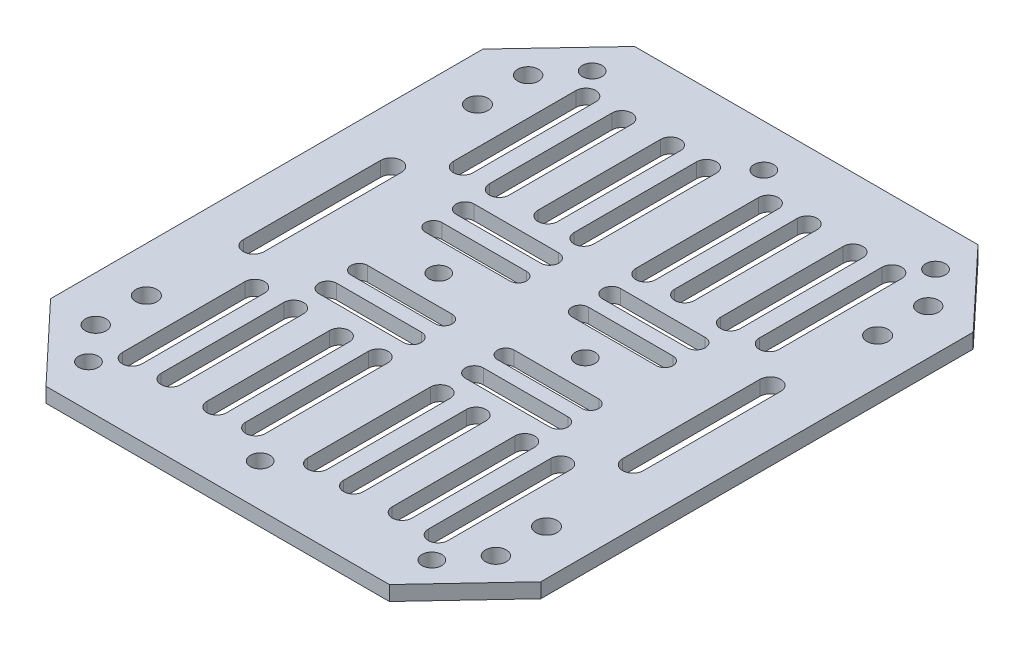
SolidWorks part; units mm, degrees
ref_plane "Front Plane" through (0, 0, 0) normal (0, 0, 1) x (1, 0, 0)
ref_plane "Top Plane" through (0, 0, 0) normal (0, 1, 0) x (1, 0, 0)
ref_plane "Right Plane" through (0, 0, 0) normal (1, 0, 0) x (0, 0, -1)
sketch "Sketch1" plane through (0, 0, 0) normal (0, 1, 0) x (1, 0, 0)
  line L0 (-19.8347, -51.3672) -> (-89.8347, -51.3672)
  line L1 (-104.8347, -35.4409) -> (-104.8347, 52.7065)
  line L2 (-19.8347, 68.6328) -> (-89.8347, 68.6328)
  line L3 (-91.3761, 22.6328) -> (-91.3761, -5.3672)
  line L4 (-95.6191, 22.6328) -> (-95.6191, -5.3672)
  line L5 (-18.2932, 22.6328) -> (-18.2932, -5.3672)
  line L6 (-89.8347, 68.6328) -> (-104.8347, 52.7065)
  line L7 (-89.8347, -51.3672) -> (-104.8347, -35.4409)
  line L8 (-80.4095, -37.3307) -> (-80.4095, -12.3238)
  line L9 (-76.3854, -37.3307) -> (-76.3854, -12.3238)
  line L10 (-88.0384, -37.6182) -> (-88.0384, -12.6112)
  line L11 (-84.0143, -37.6182) -> (-84.0143, -12.6112)
  line L12 (-63.1577, -37.3307) -> (-63.1577, -12.3238)
  line L13 (-59.1336, -37.3307) -> (-59.1336, -12.3238)
  line L14 (-70.7866, -37.6182) -> (-70.7866, -12.6112)
  line L15 (-66.7625, -37.6182) -> (-66.7625, -12.6112)
  line L16 (-61.1456, -0.641) -> (-78.3975, -0.641)
  line L17 (-61.1456, 2.7604) -> (-78.3975, 2.7604)
  line L18 (-61.1456, -7.1978) -> (-78.3975, -7.1978)
  line L19 (-61.1456, -3.5366) -> (-78.3975, -3.5366)
  line L20 (-80.4095, 54.5963) -> (-80.4095, 29.5893)
  line L21 (-76.3854, 54.5963) -> (-76.3854, 29.5893)
  line L22 (-88.0384, 54.8838) -> (-88.0384, 29.8768)
  line L23 (-84.0143, 54.8838) -> (-84.0143, 29.8768)
  line L24 (-63.1577, 54.5963) -> (-63.1577, 29.5893)
  line L25 (-59.1336, 54.5963) -> (-59.1336, 29.5893)
  line L26 (-70.7866, 54.8838) -> (-70.7866, 29.8768)
  line L27 (-66.7625, 54.8838) -> (-66.7625, 29.8768)
  line L28 (-61.1456, 17.9066) -> (-78.3975, 17.9066)
  line L29 (-61.1456, 14.5052) -> (-78.3975, 14.5052)
  line L30 (-61.1456, 24.4634) -> (-78.3975, 24.4634)
  line L31 (-61.1456, 20.8022) -> (-78.3975, 20.8022)
  line L32 (-4.8877, 52.7065) -> (-4.8877, -35.4409)
  line L33 (-29.2598, -37.3307) -> (-29.2598, -12.3238)
  line L34 (-33.2839, -37.3307) -> (-33.2839, -12.3238)
  line L35 (-21.6309, -37.6182) -> (-21.6309, -12.6112)
  line L36 (-25.655, -37.6182) -> (-25.655, -12.6112)
  line L37 (-46.5117, -37.3307) -> (-46.5117, -12.3238)
  line L38 (-50.5358, -37.3307) -> (-50.5358, -12.3238)
  line L39 (-38.8828, -37.6182) -> (-38.8828, -12.6112)
  line L40 (-42.9069, -37.6182) -> (-42.9069, -12.6112)
  line L41 (-48.5237, -0.641) -> (-31.2719, -0.641)
  line L42 (-48.5237, 2.7604) -> (-31.2719, 2.7604)
  line L43 (-48.5237, -7.1978) -> (-31.2719, -7.1978)
  line L44 (-48.5237, -3.5366) -> (-31.2719, -3.5366)
  line L45 (-29.2598, 54.5963) -> (-29.2598, 29.5893)
  line L46 (-33.2839, 54.5963) -> (-33.2839, 29.5893)
  line L47 (-21.6309, 54.8838) -> (-21.6309, 29.8768)
  line L48 (-25.655, 54.8838) -> (-25.655, 29.8768)
  line L49 (-46.5117, 54.5963) -> (-46.5117, 29.5893)
  line L50 (-50.5358, 54.5963) -> (-50.5358, 29.5893)
  line L51 (-38.8828, 54.8838) -> (-38.8828, 29.8768)
  line L52 (-42.9069, 54.8838) -> (-42.9069, 29.8768)
  line L53 (-48.5237, 17.9066) -> (-31.2719, 17.9066)
  line L54 (-48.5237, 14.5052) -> (-31.2719, 14.5052)
  line L55 (-48.5237, 24.4634) -> (-31.2719, 24.4634)
  line L56 (-48.5237, 20.8022) -> (-31.2719, 20.8022)
  line L57 (-14.0502, 22.6328) -> (-14.0502, -5.3672)
  line L58 (-19.8347, -51.3672) -> (-4.8877, -35.4409)
  line L59 (-19.8347, 68.6328) -> (-4.8877, 52.7065)
  arc A0 (-91.3761, 22.6328) -> (-95.6191, 22.6328) centre (-93.4976, 22.6328) ccw
  arc A1 (-95.6191, -5.3672) -> (-91.3761, -5.3672) centre (-93.4976, -5.3672) ccw
  circle A2 centre (-89.8347, -42.7069) radius 2
  circle A3 centre (-54.8347, -42.7069) radius 2
  arc A4 (-80.4095, -37.3307) -> (-76.3854, -37.3307) centre (-78.3975, -37.3307) ccw
  arc A5 (-76.3854, -12.3238) -> (-80.4095, -12.3238) centre (-78.3975, -12.3238) ccw
  arc A6 (-88.0384, -37.6182) -> (-84.0143, -37.6182) centre (-86.0264, -37.6182) ccw
  arc A7 (-84.0143, -12.6112) -> (-88.0384, -12.6112) centre (-86.0264, -12.6112) ccw
  arc A8 (-63.1577, -37.3307) -> (-59.1336, -37.3307) centre (-61.1456, -37.3307) ccw
  arc A9 (-59.1336, -12.3238) -> (-63.1577, -12.3238) centre (-61.1456, -12.3238) ccw
  arc A10 (-70.7866, -37.6182) -> (-66.7625, -37.6182) centre (-68.7745, -37.6182) ccw
  arc A11 (-66.7625, -12.6112) -> (-70.7866, -12.6112) centre (-68.7745, -12.6112) ccw
  arc A12 (-61.1456, -0.641) -> (-61.1456, 2.7604) centre (-61.1456, 1.0597) ccw
  arc A13 (-78.3975, 2.7604) -> (-78.3975, -0.641) centre (-78.3975, 1.0597) ccw
  arc A14 (-61.1456, -7.1978) -> (-61.1456, -3.5366) centre (-61.1456, -5.3672) ccw
  arc A15 (-78.3975, -3.5366) -> (-78.3975, -7.1978) centre (-78.3975, -5.3672) ccw
  arc A16 (-80.4095, 54.5963) -> (-76.3854, 54.5963) centre (-78.3975, 54.5963) cw
  arc A17 (-76.3854, 29.5893) -> (-80.4095, 29.5893) centre (-78.3975, 29.5893) cw
  arc A18 (-88.0384, 54.8838) -> (-84.0143, 54.8838) centre (-86.0264, 54.8838) cw
  arc A19 (-84.0143, 29.8768) -> (-88.0384, 29.8768) centre (-86.0264, 29.8768) cw
  arc A20 (-63.1577, 54.5963) -> (-59.1336, 54.5963) centre (-61.1456, 54.5963) cw
  arc A21 (-59.1336, 29.5893) -> (-63.1577, 29.5893) centre (-61.1456, 29.5893) cw
  arc A22 (-70.7866, 54.8838) -> (-66.7625, 54.8838) centre (-68.7745, 54.8838) cw
  arc A23 (-66.7625, 29.8768) -> (-70.7866, 29.8768) centre (-68.7745, 29.8768) cw
  arc A24 (-61.1456, 17.9066) -> (-61.1456, 14.5052) centre (-61.1456, 16.2059) cw
  arc A25 (-78.3975, 14.5052) -> (-78.3975, 17.9066) centre (-78.3975, 16.2059) cw
  arc A26 (-61.1456, 24.4634) -> (-61.1456, 20.8022) centre (-61.1456, 22.6328) cw
  arc A27 (-78.3975, 20.8022) -> (-78.3975, 24.4634) centre (-78.3975, 22.6328) cw
  circle A28 centre (-89.8347, 59.9725) radius 2
  circle A29 centre (-54.8347, 59.9725) radius 2
  arc A30 (-29.2598, -37.3307) -> (-33.2839, -37.3307) centre (-31.2719, -37.3307) cw
  arc A31 (-33.2839, -12.3238) -> (-29.2598, -12.3238) centre (-31.2719, -12.3238) cw
  arc A32 (-21.6309, -37.6182) -> (-25.655, -37.6182) centre (-23.643, -37.6182) cw
  arc A33 (-25.655, -12.6112) -> (-21.6309, -12.6112) centre (-23.643, -12.6112) cw
  arc A34 (-46.5117, -37.3307) -> (-50.5358, -37.3307) centre (-48.5237, -37.3307) cw
  arc A35 (-50.5358, -12.3238) -> (-46.5117, -12.3238) centre (-48.5237, -12.3238) cw
  arc A36 (-38.8828, -37.6182) -> (-42.9069, -37.6182) centre (-40.8948, -37.6182) cw
  arc A37 (-42.9069, -12.6112) -> (-38.8828, -12.6112) centre (-40.8948, -12.6112) cw
  arc A38 (-48.5237, -0.641) -> (-48.5237, 2.7604) centre (-48.5237, 1.0597) cw
  arc A39 (-31.2719, 2.7604) -> (-31.2719, -0.641) centre (-31.2719, 1.0597) cw
  arc A40 (-48.5237, -7.1978) -> (-48.5237, -3.5366) centre (-48.5237, -5.3672) cw
  arc A41 (-31.2719, -3.5366) -> (-31.2719, -7.1978) centre (-31.2719, -5.3672) cw
  arc A42 (-29.2598, 54.5963) -> (-33.2839, 54.5963) centre (-31.2719, 54.5963) ccw
  arc A43 (-33.2839, 29.5893) -> (-29.2598, 29.5893) centre (-31.2719, 29.5893) ccw
  arc A44 (-21.6309, 54.8838) -> (-25.655, 54.8838) centre (-23.643, 54.8838) ccw
  arc A45 (-25.655, 29.8768) -> (-21.6309, 29.8768) centre (-23.643, 29.8768) ccw
  arc A46 (-46.5117, 54.5963) -> (-50.5358, 54.5963) centre (-48.5237, 54.5963) ccw
  arc A47 (-50.5358, 29.5893) -> (-46.5117, 29.5893) centre (-48.5237, 29.5893) ccw
  arc A48 (-38.8828, 54.8838) -> (-42.9069, 54.8838) centre (-40.8948, 54.8838) ccw
  arc A49 (-42.9069, 29.8768) -> (-38.8828, 29.8768) centre (-40.8948, 29.8768) ccw
  arc A50 (-48.5237, 17.9066) -> (-48.5237, 14.5052) centre (-48.5237, 16.2059) ccw
  arc A51 (-31.2719, 14.5052) -> (-31.2719, 17.9066) centre (-31.2719, 16.2059) ccw
  arc A52 (-48.5237, 24.4634) -> (-48.5237, 20.8022) centre (-48.5237, 22.6328) ccw
  arc A53 (-31.2719, 20.8022) -> (-31.2719, 24.4634) centre (-31.2719, 22.6328) ccw
  circle A54 centre (-19.8347, 59.9725) radius 2
  circle A55 centre (-19.8347, -42.7069) radius 2
  circle A56 centre (-95.6191, 52.7065) radius 2.1215
  circle A57 centre (-95.6191, 42.3803) radius 2.167
  circle A58 centre (-39.8978, 8.6328) radius 2
  circle A59 centre (-69.7716, 8.6328) radius 2
  circle A60 centre (-95.6191, -25.1147) radius 2.167
  circle A61 centre (-95.6191, -35.4409) radius 2.1215
  arc A62 (-18.2932, 22.6328) -> (-14.0502, 22.6328) centre (-16.1717, 22.6328) cw
  arc A63 (-14.0502, -5.3672) -> (-18.2932, -5.3672) centre (-16.1717, -5.3672) cw
  circle A64 centre (-14.0502, -35.4409) radius 2.1215
  circle A65 centre (-14.0502, -25.1147) radius 2.167
  circle A66 centre (-14.0502, 42.3803) radius 2.167
  circle A67 centre (-14.0502, 52.7065) radius 2.1215
  dimension "D1" = 4
  dimension "D2" = 2
  dimension "D3" = 4
  dimension "D4" = 4
extrude "Boss-Extrude1" add sketch "Sketch1" along normal blind 3 contours L59 L2 L6 L1 L7 L0 L58 L32 A66 A65 A64 A60 A59 A58 A57 A56 L44 A41 L43 A40 L42 A39 L41 A38 L40 A37 L39 A36 L38 A35 L37 A34 L36 A33 L35 A32 L34
